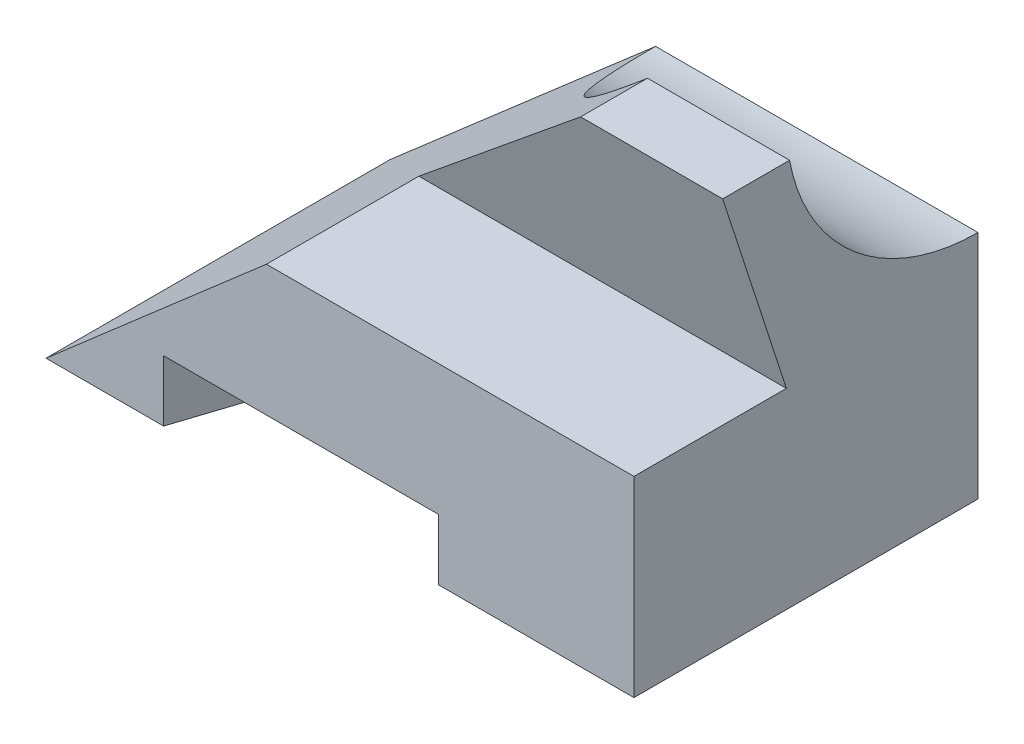
SolidWorks part; units mm, degrees
ref_plane "Front Plane" through (0, 0, 0) normal (0, 0, 1) x (1, 0, 0)
ref_plane "Top Plane" through (0, 0, 0) normal (0, 1, 0) x (1, 0, 0)
ref_plane "Right Plane" through (0, 0, 0) normal (1, 0, 0) x (0, 0, -1)
sketch "Sketch2" plane through (0, 0, 0) normal (0, 1, 0) x (1, 0, 0)
  line L1 (0, 0) -> (135, 0)
  line L2 (0, 0) -> (0, 79)
  line L3 (0, 79) -> (135, 79)
  line L4 (135, 0) -> (135, 79)
  dimension "D1" = 135
  dimension "D2" = 79
extrude "base-material" add sketch "Sketch2" along normal blind 89
sketch "Sketch3" plane through (135, 0, 0) normal (1, 0, 0) x (0, 0, -1)
  line L0 (0, 0) -> (79, 0) construction
  line L1 (79, 0) -> (79, 89) construction
  line L2 (35.7334, 89) -> (79, 89)
  line L3 (0, 89) -> (79, 89) construction
  line L4 (79, 89) -> (79, 53)
  line L5 (0, 0) -> (0, 44) construction
  line L6 (0, 89) -> (0, 0) construction
  line L7 (0, 44) -> (35, 44)
  line L8 (35, 44) -> (20.3786, 89)
  line L9 (0, 44) -> (0, 89)
  line L10 (0, 89) -> (20.3786, 89)
  arc A0 (35.7334, 89) -> (79, 53) centre (79, 97) ccw
  dimension "D1" = 44
  dimension "D2" = 44
  dimension "D3" = 35
  dimension "D4" = 72
extrude "thru-all-cuts" cut sketch "Sketch3" against normal through all
ref_plane "Plane1" through (0, 0, -20.3786) normal (0, 0, 1) x (1, 0, 0)
sketch "Sketch5" plane through (0, 0, -20.3786) normal (0, 0, 1) x (1, 0, 0)
  line L0 (0, 0) -> (102.3828, 89)
  line L1 (0, 89) -> (135, 89) construction
  line L2 (0, 0) -> (135, 0) construction
  line L3 (0, 0) -> (0, 89)
  line L4 (0, 89) -> (102.3828, 89)
  dimension "D1" = 139
extrude "angle-thru-all" cut sketch "Sketch5" against normal through all and the other way through all
sketch "Sketch7" plane through (0, 0, 0) normal (0, -1, 0) x (1, 0, 0)
  line L0 (27, 0) -> (52.6687, -79)
  line L1 (0, 0) -> (135, 0) construction
  line L2 (135, -79) -> (0, -79) construction
  line L3 (90.0877, 0) -> (115.7564, -79)
  line L4 (60.9695, -79) -> (135, -79) construction
  line L5 (0, 0) -> (50.6162, 0) construction
  line L6 (27, 0) -> (90.0877, 0)
  line L7 (52.6687, -79) -> (115.7564, -79)
  dimension "D1" = 27
  dimension "D2" = 60
  dimension "D3" = 108
extrude "Cut-Extrude3" cut sketch "Sketch7" against normal blind 14
